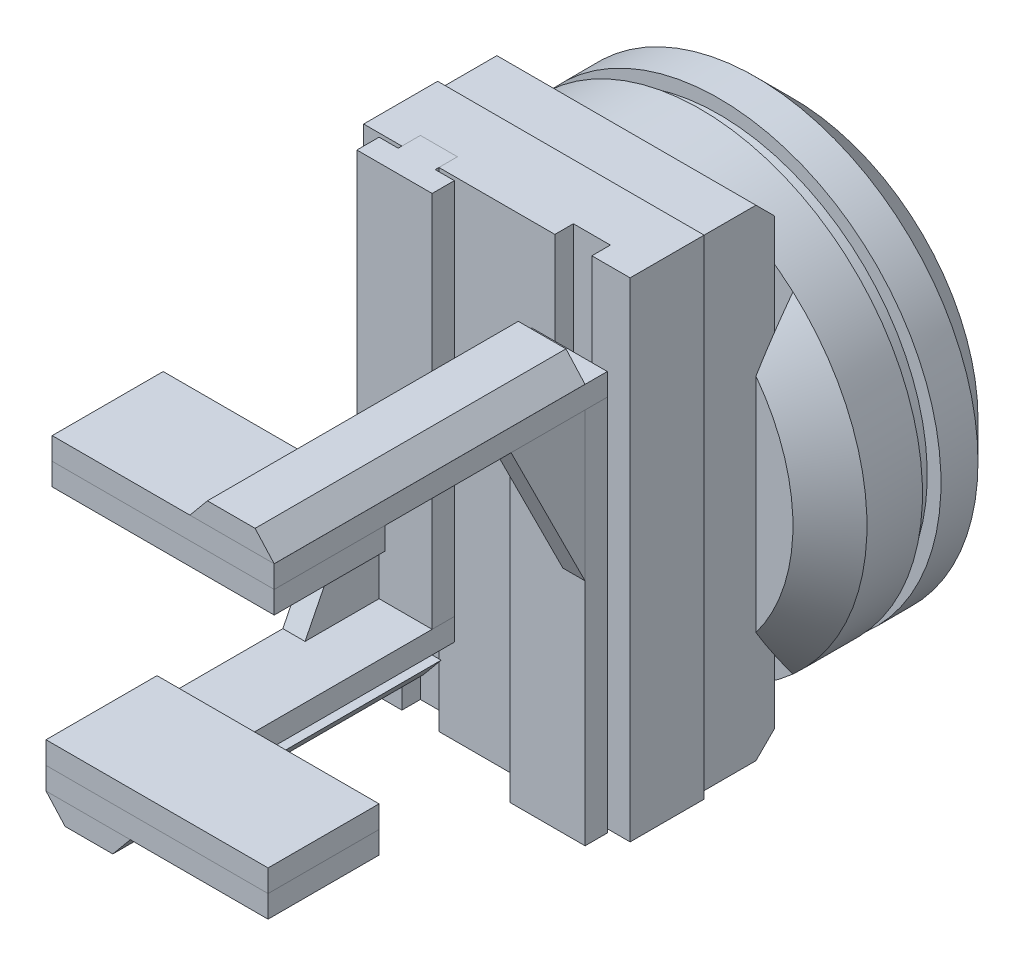
SolidWorks part; units mm, degrees
ref_plane "Front Plane" through (0, 0, 0) normal (0, 0, 1) x (1, 0, 0)
ref_plane "Top Plane" through (0, 0, 0) normal (0, 1, 0) x (1, 0, 0)
ref_plane "Right Plane" through (0, 0, 0) normal (1, 0, 0) x (0, 0, -1)
sketch "Sketch1" plane through (0, 0, 0) normal (0, 0, 1) x (1, 0, 0)
  circle A0 centre (0, 0) radius 60
  dimension "D1" = 120
extrude "Boss-Extrude1" add sketch "Sketch1" along normal blind 50
sketch "Sketch2" plane through (0, 0, 50) normal (0, 0, 1) x (1, 0, 0)
  line L1 (-40, 219.8876) -> (40, 219.8876)
  line L2 (-40, 219.8876) -> (-40, -219.8876)
  line L3 (-40, -219.8876) -> (40, -219.8876)
  line L4 (40, 219.8876) -> (40, -219.8876)
  line L5 (-40, 219.8876) -> (40, -219.8876) construction
  line L6 (-40, -219.8876) -> (40, 219.8876) construction
  point P0 (0, 0)
  dimension "D1" = 80
extrude "Cut-Extrude1" cut sketch "Sketch2" against normal blind 10
sketch "Sketch3" plane through (0, 0, 40) normal (0, 0, 1) x (1, 0, 0)
  line L1 (-35, 65) -> (35, 65)
  line L2 (-35, 65) -> (-35, -65)
  line L3 (-35, -65) -> (35, -65)
  line L4 (35, 65) -> (35, -65)
  line L5 (-35, 65) -> (35, -65) construction
  line L6 (-35, -65) -> (35, 65) construction
  point P0 (0, 0)
  dimension "D1" = 70
  dimension "D2" = 130
extrude "Boss-Extrude2" add sketch "Sketch3" along normal blind 20 separate body
sketch "Sketch4" plane through (0, 0, 60) normal (0, 0, 1) x (1, 0, 0)
  line L8 (36, -66) -> (36, 66)
  line L9 (36, 66) -> (-36, 66)
  line L10 (-36, 66) -> (-36, -66)
  line L11 (-36, -66) -> (36, -66)
  line L12 (36, -66) -> (36, 66)
  line L13 (36, 66) -> (-36, 66)
  line L14 (-36, 66) -> (-36, -66)
  line L15 (-36, -66) -> (36, -66)
  dimension "D1" = 1
extrude "Boss-Extrude3" add sketch "Sketch4" along normal blind 20 separate body
sketch "Sketch5" plane through (0, -66, 0) normal (0, -1, 0) x (1, 0, 0)
  line L0 (-20.6654, 80) -> (0, 80) construction
  line L1 (-36, 80) -> (36, 80) construction
  line L2 (0, 80) -> (20.6654, 80) construction
  line L4 (-25.6654, 85) -> (-15.6654, 85)
  line L5 (-25.6654, 85) -> (-25.6654, 75)
  line L6 (-25.6654, 75) -> (-15.6654, 75)
  line L7 (-15.6654, 85) -> (-15.6654, 75)
  line L8 (-25.6654, 85) -> (-15.6654, 75) construction
  line L9 (-25.6654, 75) -> (-15.6654, 85) construction
  line L10 (15.6654, 85) -> (25.6654, 85)
  line L11 (15.6654, 85) -> (15.6654, 75)
  line L12 (15.6654, 75) -> (25.6654, 75)
  line L13 (25.6654, 85) -> (25.6654, 75)
  line L14 (15.6654, 85) -> (25.6654, 75) construction
  line L15 (15.6654, 75) -> (25.6654, 85) construction
  dimension "D1" = 10
extrude "Cut-Extrude2" cut sketch "Sketch5" against normal through all
sketch "Sketch6" plane through (0, 0, 75) normal (0, 0, 1) x (1, 0, 0)
  line L0 (25.6654, -66) -> (25.6654, 66) construction
  line L1 (15.6654, -66) -> (25.6654, -66)
  line L2 (15.6654, -66) -> (15.6654, 36)
  line L3 (15.6654, 36) -> (25.6654, 36)
  line L4 (25.6654, -66) -> (25.6654, 36)
  line L5 (36, 66) -> (25.6654, 66) construction
  point P7 (30.8327, 66)
  dimension "D1" = 30
extrude "Boss-Extrude4" add sketch "Sketch6" along normal blind 6 separate body
sketch "Sketch7" plane through (0, 0, 81) normal (0, 0, 1) x (1, 0, 0)
  line L0 (25.6654, -66) -> (36, -66) construction
  line L1 (10.4981, 36) -> (30.8327, 36)
  line L2 (10.4981, 36) -> (10.4981, -66)
  line L3 (10.4981, -66) -> (30.8327, -66)
  line L4 (30.8327, 36) -> (30.8327, -66)
  line L5 (10.4981, 36) -> (30.8327, -66) construction
  line L6 (10.4981, -66) -> (30.8327, 36) construction
  line L7 (25.6654, -15) -> (15.6654, -15) construction
  line L8 (25.6654, -66) -> (25.6654, 36) construction
  line L9 (15.6654, 36) -> (15.6654, -66) construction
  point P0 (20.6654, -15)
extrude "Boss-Extrude5" add sketch "Sketch7" along normal blind 6
sketch "Sketch9" plane through (0, 36, 0) normal (0, 1, 0) x (1, 0, 0)
  line L0 (30.8327, -81) -> (30.8327, -171)
  line L1 (30.8327, -171) -> (-29.1673, -171)
  line L2 (-29.1673, -171) -> (-29.1673, -141)
  line L3 (-29.1673, -141) -> (10.4981, -141)
  line L4 (10.4981, -141) -> (10.4981, -81)
  line L5 (10.4981, -81) -> (30.8327, -81)
  dimension "D1" = 60
  dimension "D2" = 60
  dimension "D3" = 90
extrude "Boss-Extrude6" add sketch "Sketch9" along normal blind 6 separate body
sketch "Sketch10" plane through (0, 36, 0) normal (0, -1, 0) x (1, 0, 0)
  line L0 (10.4981, 141) -> (-29.1673, 141) construction
  line L1 (-29.1673, 171) -> (30.8327, 171)
  line L2 (-29.1673, 171) -> (-29.1673, 141)
  line L3 (-29.1673, 141) -> (30.8327, 141)
  line L4 (30.8327, 171) -> (30.8327, 141)
  line L5 (30.8327, 171) -> (30.8327, 81) construction
extrude "Boss-Extrude7" add sketch "Sketch10" along normal blind 6 separate body
sketch "Sketch11" plane through (30.8327, 0, 0) normal (1, 0, 0) x (0, 0, -1)
  line L0 (-107, 36) -> (-87, -4)
  line L1 (-171, 36) -> (-81, 36) construction
  line L2 (-87, -66) -> (-87, 36) construction
  line L3 (-87, -4) -> (-87, 36)
  line L4 (-87, 36) -> (-107, 36)
  dimension "D1" = 20
  dimension "D2" = 40
extrude "Boss-Extrude8" add sketch "Sketch11" against normal blind 6 separate body
sketch "Sketch12" plane through (0, 0, 171) normal (0, 0, 1) x (1, 0, 0)
  line L0 (30.8186, 42) -> (25.6654, 47.7163)
  line L1 (-29.1673, 42) -> (30.8327, 42) construction
  line L2 (25.6654, -66) -> (25.6654, 66) construction
  line L3 (25.6654, 47.7163) -> (12.7827, 47.7163)
  line L4 (12.7827, 47.7163) -> (8.0549, 42)
  line L5 (8.0549, 42) -> (30.8186, 42)
extrude "Boss-Extrude9" add sketch "Sketch12" against normal blind 84 separate body
pattern_circular "CirPattern1" count 2 over 360 about axis through (0, 0, 0) along (0, 0, 1) of bodies 115 107 110 108 109
sketch "Sketch13" plane through (0, 0, 0) normal (0, 0, -1) x (-1, 0, 0)
  circle A0 centre (0, 0) radius 60
  circle A1 centre (0, 0) radius 56.2878
extrude "Cut-Extrude3" cut sketch "Sketch13" against normal blind 5 from offset 20 offset against normal yes
chamfer "Chamfer1" distance 10 angle 45 1 edges at (60, 0, 0)
sketch "Sketch14" plane through (0, 0, 0) normal (0, 0, -1) x (-1, 0, 0)
  circle A0 centre (0, 0) radius 30
  dimension "D1" = 60
extrude "Cut-Extrude4" cut sketch "Sketch14" against normal blind 5
sketch "Sketch15" plane through (0, 0, 0) normal (0, 0, -1) x (-1, 0, 0)
  circle A0 centre (0, 0) radius 30
  circle A1 centre (0, 0) radius 35
  dimension "D1" = 5
extrude "Boss-Extrude10" add sketch "Sketch15" along normal blind 5 separate body
chamfer "Chamfer2" distance 10 angle 45 1 edges at (60, 0, 50)
chamfer "Chamfer3" distance 10 angle 45 1 edges at (-60, 0, 50)
chamfer "Chamfer4" distance 5 angle 45 2 edges at (0, 65, 40) (0, -65, 40)
